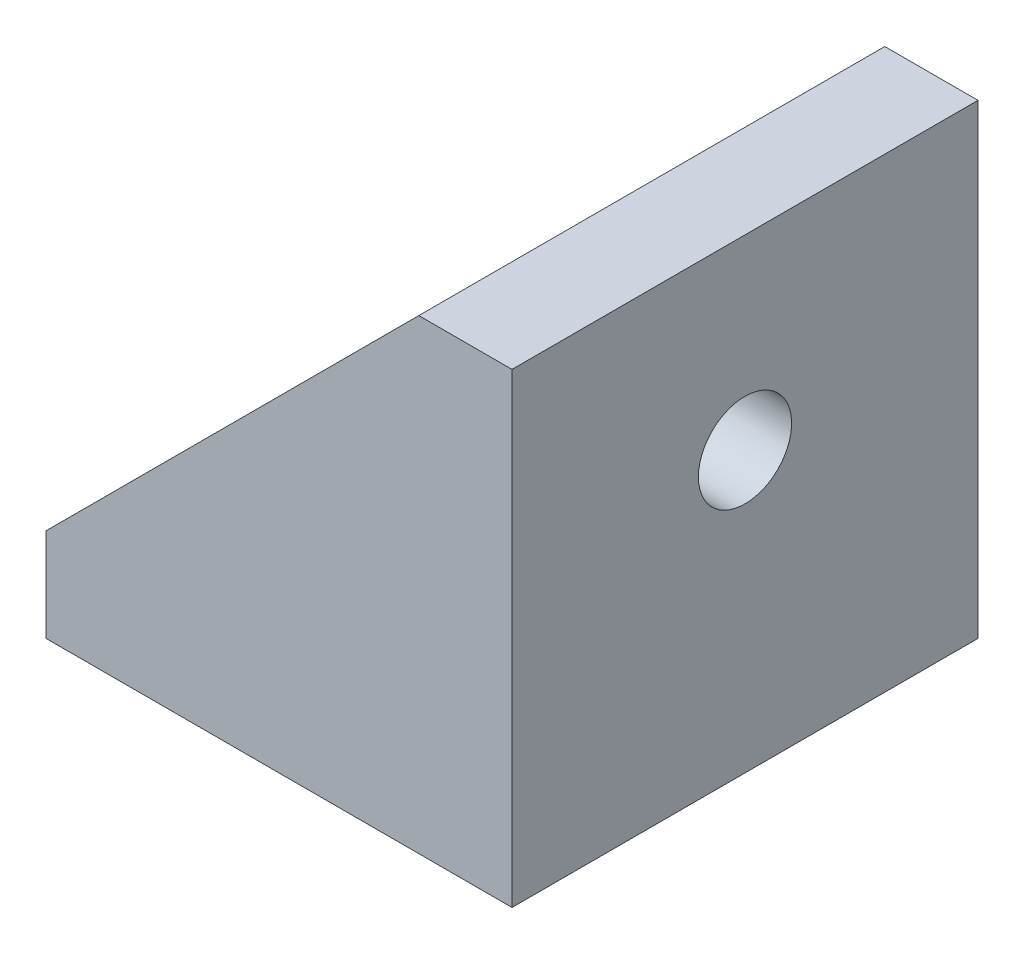
SolidWorks part; units mm, degrees
ref_plane "Front Plane" through (0, 0, 0) normal (0, 0, 1) x (1, 0, 0)
ref_plane "Top Plane" through (0, 0, 0) normal (0, 1, 0) x (1, 0, 0)
ref_plane "Right Plane" through (0, 0, 0) normal (1, 0, 0) x (0, 0, -1)
sketch "Sketch1" plane through (0, 0, 0) normal (0, 0, 1) x (1, 0, 0)
  line L0 (0, 0) -> (-20, 0)
  line L1 (55, 0) -> (-55, 0) construction
  line L2 (-20, 0) -> (-20, 4)
  line L3 (-20, 4) -> (-4, 4)
  line L4 (-4, 4) -> (-4, 20)
  line L5 (-4, 20) -> (0, 20)
  line L6 (0, -55) -> (0, 55) construction
  line L7 (0, 20) -> (0, 0)
extrude "Boss-Extrude1" add sketch "Sketch1" along normal blind 20
sketch "Sketch2" plane through (0, 0, 0) normal (0, 0, -1) x (-1, 0, 0)
  line L0 (4, 20) -> (20, 4)
  line L1 (20, 4) -> (4, 4)
  line L2 (4, 4) -> (20, 4) construction
  line L3 (4, 20) -> (4, 4) construction
  line L4 (4, 4) -> (4, 20)
extrude "Boss-Extrude2" add sketch "Sketch2" against normal blind 4
sketch "Sketch3" plane through (0, 0, 20) normal (0, 0, 1) x (1, 0, 0)
  line L0 (-4, 20) -> (-20, 4)
  line L1 (-20, 4) -> (-4, 4)
  line L2 (-4, 4) -> (-4, 20)
extrude "Boss-Extrude3" add sketch "Sketch3" against normal blind 4 contours L0 L1 L2
sketch "Sketch4" plane through (0, 4, 0) normal (0, 1, 0) x (1, 0, 0)
  line L0 (-4, -10) -> (-20, -10) construction
  line L1 (-4, -16) -> (-4, -4) construction
  line L2 (-20, -16) -> (-20, -4) construction
  circle A0 centre (-12, -10) radius 2
extrude "Cut-Extrude1" cut sketch "Sketch4" against normal blind 4
sketch "Sketch5" plane through (-4, 0, 0) normal (-1, 0, 0) x (0, 0, 1)
  line L0 (10, 4) -> (10, 20) construction
  line L1 (16, 4) -> (4, 4) construction
  line L2 (16, 20) -> (4, 20) construction
  circle A0 centre (10, 12) radius 2
extrude "Cut-Extrude2" cut sketch "Sketch5" against normal blind 4
